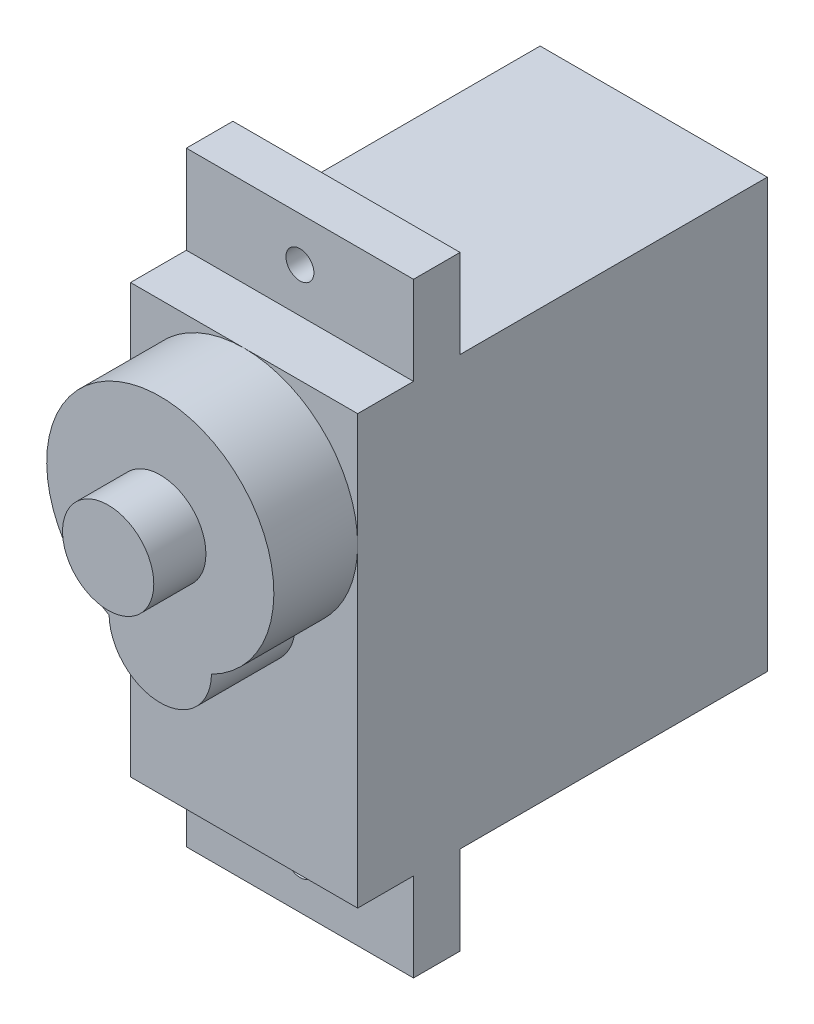
SolidWorks part; units mm, degrees
ref_plane "Plan de face" through (0, 0, 0) normal (0, 0, 1) x (1, 0, 0)
ref_plane "Plan de dessus" through (0, 0, 0) normal (0, 1, 0) x (1, 0, 0)
ref_plane "Plan de droite" through (0, 0, 0) normal (1, 0, 0) x (0, 0, -1)
sketch "Esquisse1" plane through (0, 0, 0) normal (1, 0, 0) x (0, 0, -1)
  line L1 (11, -11.5) -> (-11, -11.5)
  line L2 (11, -11.5) -> (11, 11.5)
  line L3 (11, 11.5) -> (-11, 11.5)
  line L4 (-11, -11.5) -> (-11, 11.5)
  line L5 (11, -11.5) -> (-11, 11.5) construction
  line L6 (11, 11.5) -> (-11, -11.5) construction
  point P0 (0, 0)
  dimension "D1" = 22
  dimension "D2" = 23
extrude "Boss.-Extru.1" add sketch "Esquisse1" along normal mid plane 12.2
sketch "Esquisse2" plane through (0, 0, 11) normal (0, 0, 1) x (1, 0, 0)
  line L1 (6.1, 11.5) -> (-6.1, 11.5) construction
  line L2 (-6.1, 11.5) -> (-6.1, -11.5) construction
  arc A0 (2.7496, -0.0451) -> (-2.7496, -0.0451) centre (0, 5.4) ccw
  arc A1 (-2.7496, -0.0451) -> (2.7496, -0.0451) centre (0, 0) ccw
  dimension "D1" = 2.75
extrude "Boss.-Extru.2" add sketch "Esquisse2" along normal blind 4.5
sketch "Esquisse3" plane through (0, 0, 15.5) normal (0, 0, 1) x (1, 0, 0)
  circle A0 centre (0, 5.4) radius 2.45
  arc A1 (2.7496, -0.0451) -> (-2.7496, -0.0451) centre (0, 5.4) ccw construction
  dimension "D1" = 4.9
extrude "Boss.-Extru.3" add sketch "Esquisse3" along normal blind 2.8
sketch "Esquisse4" plane through (0, 0, 0) normal (1, 0, 0) x (0, 0, -1)
  line L0 (11, 11.5) -> (-11, 11.5) construction
  line L1 (-8, 11.5) -> (-5.5, 11.5)
  line L2 (-8, 11.5) -> (-8, 16.25)
  line L3 (-8, 16.25) -> (-5.5, 16.25)
  line L4 (-5.5, 11.5) -> (-5.5, 16.25)
  line L5 (-11, -11.5) -> (11, -11.5) construction
  line L6 (-8, -11.5) -> (-5.5, -11.5)
  line L7 (-8, -11.5) -> (-8, -16.25)
  line L8 (-8, -16.25) -> (-5.5, -16.25)
  line L9 (-5.5, -11.5) -> (-5.5, -16.25)
  line L10 (11, -11.5) -> (11, 11.5) construction
  dimension "D1" = 32.5
  dimension "D2" = 16.5
  dimension "D3" = 2.5
extrude "Boss.-Extru.4" add sketch "Esquisse4" along normal mid plane 12.2
sketch "Esquisse5" plane through (0, 0, 8) normal (0, 0, 1) x (1, 0, 0)
  line L0 (-6.1, 16.25) -> (6.1, 11.5) construction
  line L1 (-6.1, -11.5) -> (6.1, -16.25) construction
  circle A0 centre (0, 13.875) radius 0.75
  circle A1 centre (0, -13.875) radius 0.75
  dimension "D1" = 1.5
extrude "Enlèv. mat.-Extru.1" cut sketch "Esquisse5" against normal up to next
